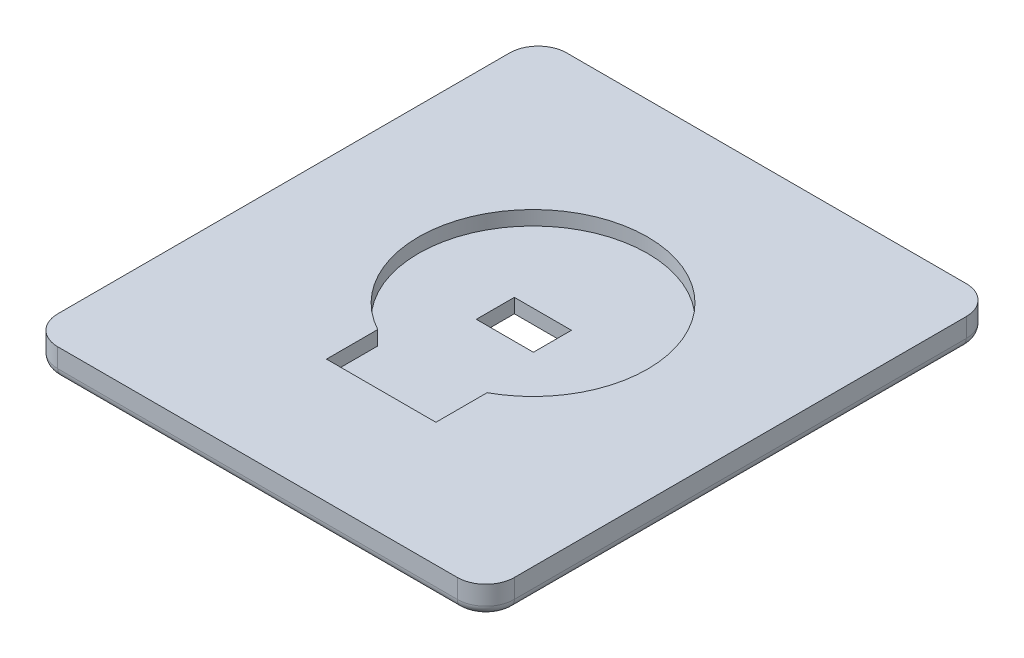
SolidWorks part; units mm, degrees
ref_plane "Front Plane" through (0, 0, 0) normal (0, 0, 1) x (1, 0, 0)
ref_plane "Top Plane" through (0, 0, 0) normal (0, 1, 0) x (1, 0, 0)
ref_plane "Right Plane" through (0, 0, 0) normal (1, 0, 0) x (0, 0, -1)
sketch "Sketch1" plane through (0, 0, 0) normal (0, 1, 0) x (1, 0, 0)
  line L0 (-34.1313, 26.75) -> (38.5187, 26.75) construction
  line L1 (-21, -23.75) -> (21, -23.75)
  line L2 (-21, -23.75) -> (-21, 23.75)
  line L3 (-21, 23.75) -> (21, 23.75)
  line L4 (21, -23.75) -> (21, 23.75)
  line L5 (-21, -23.75) -> (21, 23.75) construction
  line L6 (-21, 23.75) -> (21, -23.75) construction
  line L7 (-24, 31.8657) -> (-24, -25.8166) construction
  line L8 (-41.3088, -26.75) -> (35.4551, -26.75) construction
  line L9 (24, 16.9856) -> (24, -22.2279) construction
  point P0 (0, 0)
  point P11 (-24, -26.75)
  point P15 (-24, 26.75)
  point P16 (24, 26.75)
  dimension "D1" = 42
  dimension "D2" = 47.5
  dimension "D3" = 3
  dimension "D4" = 3
  dimension "D5" = 3
  dimension "D6" = 3
extrude "Boss-Extrude1" add sketch "Sketch1" along normal blind 3
ref_plane "Plane1" through (0, 3, 0) normal (0, 1, 0) x (1, 0, 0)
sketch "Sketch2" plane through (0, 3, 0) normal (0, 1, 0) x (1, 0, 0)
  line L0 (-10.479, 23.75) -> (33.8658, 23.75) construction
  line L2 (-7.0091, -23.75) -> (43.859, -23.75) construction
  line L4 (21, 10.2361) -> (21, 29.1121) construction
  line L6 (-21, 14.7469) -> (-21, 27.863) construction
  line L8 (12, 45.205) -> (12, -33.8048) construction
  line L9 (5.75, 40.8431) -> (5.75, -31.723) construction
  line L10 (3, 39.6535) -> (3, -32.5161) construction
  line L11 (-5.75, 44.3128) -> (-5.75, -32.5161) construction
  line L12 (-12, 37.3734) -> (-12, -35.7875) construction
  line L13 (-3, 35.4899) -> (-3, -32.5161) construction
  line L14 (-43.1956, 14.25) -> (44.381, 14.25) construction
  line L15 (43.7902, 3.25) -> (-40.6111, 3.25) construction
  line L16 (43.7902, -0.75) -> (-41.0542, -0.75) construction
  line L17 (43.1995, -7.75) -> (-29.1656, -7.75) construction
  line L18 (33.7477, -13.75) -> (-42.7525, -13.75) construction
  line L19 (-13.8596, 1.25) -> (28.5261, 1.25) construction
  line L24 (-5.75, -13.75) -> (5.75, -13.75)
  line L25 (-5.75, -13.75) -> (-5.75, -7.75)
  line L26 (-5.75, -7.75) -> (5.75, -7.75)
  line L27 (5.75, -13.75) -> (5.75, -7.75)
  line L28 (0, 19.0822) -> (0, -3.8695) construction
  circle A1 centre (0, 2.2115) radius 12.0385
  point P29 (-3, 3.25)
  point P31 (3, 3.25)
  point P32 (3, -0.75)
  point P33 (-3, -0.75)
  point P34 (-5.75, -7.75)
  point P35 (5.75, -7.75)
  point P40 (-5.75, -13.75)
  point P41 (5.75, -13.75)
  point P49 (-12, 1.25)
  point P53 (12, 1.25)
  point P54 (0, 14.25)
  dimension "D1" = 9
  dimension "D2" = 9
  dimension "D3" = 6.25
  dimension "D4" = 9
  dimension "D5" = 6.25
  dimension "D6" = 9
  dimension "D7" = 10
  dimension "D8" = 16
  dimension "D9" = 13
  dimension "D10" = 4
  dimension "D11" = 38
  dimension "D12" = 2
extrude "Cut-Extrude2" cut sketch "Sketch2" against normal blind 1.5 contours L27 A1 L25 L26 | A1 L25 L24 L27 | L25 A1 L27 L26
sketch "Sketch3" plane through (0, 3, 0) normal (0, 1, 0) x (1, 0, 0)
  line L0 (-3, 3.25) -> (35.0456, 3.25) construction
  line L2 (-3, -0.75) -> (40.1116, -0.75) construction
  line L4 (-3, 5.7817) -> (-3, -6.9249) construction
  line L6 (3, -3.0042) -> (3, 10.836) construction
  line L9 (-3, -0.75) -> (3, -0.75)
  line L10 (-3, -0.75) -> (-3, 3.25)
  line L11 (-3, 3.25) -> (3, 3.25)
  line L12 (3, -0.75) -> (3, 3.25)
  point P7 (-3, 3.25)
  point P9 (3, 3.25)
  point P11 (3, -0.75)
  point P13 (-3, -0.75)
extrude "Cut-Extrude3" cut sketch "Sketch3" against normal blind 5
sketch "Sketch4" plane through (0, 0, 0) normal (0, 1, 0) x (1, 0, 0)
  line L1 (-24, -26.75) -> (24, -26.75)
  line L2 (-24, -26.75) -> (-24, 26.75)
  line L3 (-24, 26.75) -> (24, 26.75)
  line L4 (24, -26.75) -> (24, 26.75)
  line L5 (-21, 23.75) -> (21, 23.75)
  line L6 (-21, 23.75) -> (-21, -23.75)
  line L7 (-21, -23.75) -> (21, -23.75)
  line L8 (21, 23.75) -> (21, -23.75)
extrude "Boss-Extrude2" add sketch "Sketch4" along normal blind 3
fillet "Fillet1" radius 3 4 edges at (-24, 1.5, -26.75) (24, 1.5, -26.75) (24, 1.5, 26.75) (-24, 1.5, 26.75)
fillet "Fillet2" radius 1 8 edges at (0, 0, 26.75) (23.1213, 0, 25.8713) (24, 0, 0) (23.1213, 0, -25.8713) (0, 0, -26.75) (-23.1213, 0, -25.8713) (-24, 0, 0) (-23.1213, 0, 25.8713)
